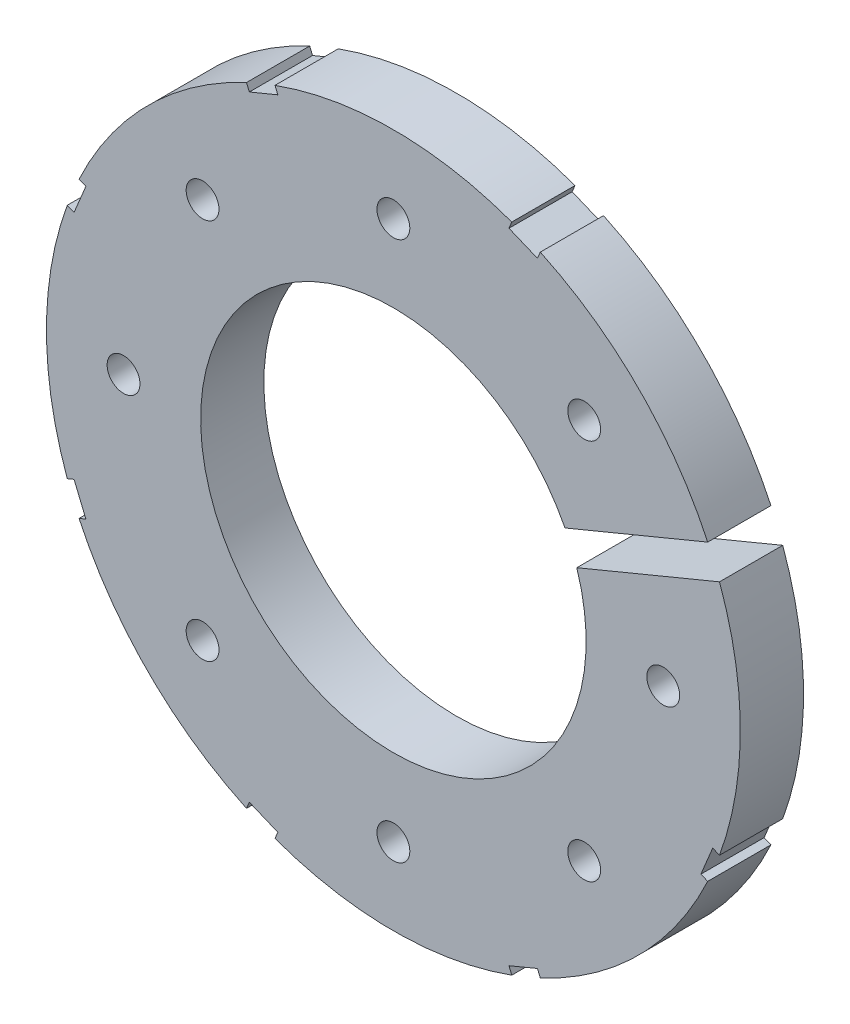
SolidWorks part; units mm, degrees
material "Brass"
ref_plane "Front Plane" through (0, 0, 0) normal (0, 0, 1) x (1, 0, 0)
ref_plane "Top Plane" through (0, 0, 0) normal (0, 1, 0) x (1, 0, 0)
ref_plane "Right Plane" through (0, 0, 0) normal (1, 0, 0) x (0, 0, -1)
sketch "Sketch4" plane through (0, 0, 0) normal (0, 0, 1) x (1, 0, 0)
  circle A0 centre (0, 0) radius 28.575
  dimension "D1" = 57.15
extrude "Boss-Extrude2" add sketch "Sketch4" along normal blind 5.207
sketch "Sketch5" plane through (0, 0, 5.207) normal (0, 0, 1) x (1, 0, 0)
  circle A0 centre (0, 0) radius 15.875
  circle A1 centre (0, 0) radius 28.575 construction
  dimension "D1" = 12.7
extrude "Cut-Extrude5" cut sketch "Sketch5" against normal through all
sketch "Sketch8" plane through (0, 0, 5.207) normal (0, 0, 1) x (1, 0, 0)
  line L0 (32.3671, 14.7815) -> (13.5939, 7.0054)
  line L1 (32.3671, 14.7815) -> (33.3392, 12.4349)
  line L2 (13.5939, 7.0054) -> (14.5659, 4.6588)
  line L3 (33.3392, 12.4349) -> (14.5659, 4.6588)
  line L4 (32.3671, 14.7815) -> (14.5659, 4.6588) construction
  line L5 (13.5939, 7.0054) -> (33.3392, 12.4349) construction
  line L6 (0, 0) -> (50.4438, 0) construction
  line L7 (12.3515, 26.5005) -> (10.0049, 27.4725)
  line L8 (12.3515, 26.5005) -> (11.8655, 25.3272)
  line L9 (10.0049, 27.4725) -> (9.5188, 26.2992)
  line L10 (11.8655, 25.3272) -> (9.5188, 26.2992)
  line L11 (10.0049, 27.4725) -> (11.8655, 25.3272) construction
  line L12 (12.3515, 26.5005) -> (9.5188, 26.2992) construction
  line L13 (-10.0049, 27.4725) -> (-12.3515, 26.5005)
  line L14 (-10.0049, 27.4725) -> (-9.5188, 26.2992)
  line L15 (-9.5188, 26.2992) -> (-11.8655, 25.3272)
  line L16 (-12.3515, 26.5005) -> (-11.8655, 25.3272)
  line L17 (-10.0049, 27.4725) -> (-11.8655, 25.3272) construction
  line L18 (-12.3515, 26.5005) -> (-9.5188, 26.2992) construction
  line L19 (-26.5005, 12.3515) -> (-27.4725, 10.0049)
  line L20 (-26.5005, 12.3515) -> (-25.3272, 11.8655)
  line L21 (-25.3272, 11.8655) -> (-26.2992, 9.5188)
  line L22 (-27.4725, 10.0049) -> (-26.2992, 9.5188)
  line L23 (-26.5005, 12.3515) -> (-26.2992, 9.5188) construction
  line L24 (-27.4725, 10.0049) -> (-25.3272, 11.8655) construction
  line L25 (-27.4725, -10.0049) -> (-26.5005, -12.3515)
  line L26 (-27.4725, -10.0049) -> (-26.2992, -9.5188)
  line L27 (-26.2992, -9.5188) -> (-25.3272, -11.8655)
  line L28 (-26.5005, -12.3515) -> (-25.3272, -11.8655)
  line L29 (-27.4725, -10.0049) -> (-25.3272, -11.8655) construction
  line L30 (-26.5005, -12.3515) -> (-26.2992, -9.5188) construction
  line L31 (-12.3515, -26.5005) -> (-10.0049, -27.4725)
  line L32 (-12.3515, -26.5005) -> (-11.8655, -25.3272)
  line L33 (-11.8655, -25.3272) -> (-9.5188, -26.2992)
  line L34 (-10.0049, -27.4725) -> (-9.5188, -26.2992)
  line L35 (-12.3515, -26.5005) -> (-9.5188, -26.2992) construction
  line L36 (-10.0049, -27.4725) -> (-11.8655, -25.3272) construction
  line L37 (10.0049, -27.4725) -> (12.3515, -26.5005)
  line L38 (10.0049, -27.4725) -> (9.5188, -26.2992)
  line L39 (9.5188, -26.2992) -> (11.8655, -25.3272)
  line L40 (12.3515, -26.5005) -> (11.8655, -25.3272)
  line L41 (10.0049, -27.4725) -> (11.8655, -25.3272) construction
  line L42 (12.3515, -26.5005) -> (9.5188, -26.2992) construction
  line L43 (26.5005, -12.3515) -> (27.4725, -10.0049)
  line L44 (26.5005, -12.3515) -> (25.3272, -11.8655)
  line L45 (25.3272, -11.8655) -> (26.2992, -9.5188)
  line L46 (27.4725, -10.0049) -> (26.2992, -9.5188)
  line L47 (26.5005, -12.3515) -> (26.2992, -9.5188) construction
  line L48 (27.4725, -10.0049) -> (25.3272, -11.8655) construction
  circle A0 centre (0, 0) radius 15.875 construction
  circle A1 centre (0, 0) radius 28.575 construction
  point P1 (23.4665, 9.7202)
  point P3 (10.9352, 26.3999)
  point P11 (-10.9352, 26.3999)
  point P20 (-26.3999, 10.9352)
  point P25 (-26.3999, -10.9352)
  point P26 (0, 0)
  point P31 (-10.9352, -26.3999)
  point P36 (10.9352, -26.3999)
  point P41 (26.3999, -10.9352)
  point P46 (0, 0)
  dimension "D1" = 20.32
  dimension "D2" = 9.525
  dimension "D3" = 2.54
  dimension "D4" = 22.5
  dimension "D5" = 1.27
  dimension "D6" = 2.54
  dimension "D7" = 1.27
  dimension "D8" = 1.27
  dimension "D9" = 0.635
  dimension "D10" = 67.5
  dimension "D12" = 0.635
  dimension "D13" = 22.5
  dimension "D11" = 7
extrude "Cut-Extrude11" cut sketch "Sketch8" against normal through all
hole_wizard "#6-32 Tapped Hole1" positions "Sketch10" profile "Sketch9" tap size "#6-32" standard "ANSI Inch" end condition through all
sketch "Sketch10" plane through (0, 0, 5.207) normal (0, 0, 1) x (1, 0, 0)
  line L0 (0, 0) -> (22.225, 0) construction
  line L2 (0, 0) -> (15.7154, 15.7154) construction
  line L4 (0, 0) -> (15.7154, -15.7154) construction
  arc A0 (14.1336, 7.229) -> (15.1056, 4.8823) centre (0, 0) ccw construction
  point P0 (22.225, 0)
  point P10 (15.7154, -15.7154)
  point P11 (0, -22.225)
  point P12 (-15.7154, -15.7154)
  point P13 (-22.225, 0)
  point P14 (-15.7154, 15.7154)
  point P15 (0, 22.225)
  point P16 (15.7154, 15.7154)
  dimension "D1" = 6.35
  dimension "D3" = 45
  dimension "D4" = 45
  dimension "D5" = 6.35
  dimension "D2" = 8
cosmetic thread "Hole Thread1" parameters "D2"=3.5052
cosmetic thread "Hole Thread2" parameters "D2"=3.5052
cosmetic thread "Hole Thread3" parameters "D2"=3.5052
cosmetic thread "Hole Thread4" parameters "D2"=3.5052
cosmetic thread "Hole Thread5" parameters "D2"=3.5052
cosmetic thread "Hole Thread6" parameters "D2"=3.5052
cosmetic thread "Hole Thread7" parameters "D2"=3.5052
cosmetic thread "Hole Thread8" parameters "D2"=3.5052
sketch "Sketch9" plane through (22.225, 0, 5.207) normal (1, 0, 0) x (0, -1, 0)
  line L0 (0, 0) -> (0, 5.207)
  line L1 (0, 5.207) -> (1.3525, 5.207)
  line L2 (1.3525, 5.207) -> (1.3525, 0)
  line L5 (1.3525, 0) -> (0, 0)
  line L11 (0, -6.35) -> (0, 107.95) construction
  dimension "Thru Tap Drill Dia." = 2.7051
  dimension "Thru Tap Drill Depth" = 5.207
